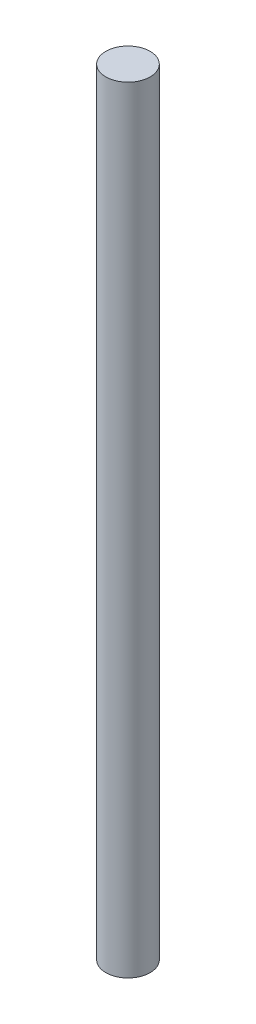
SolidWorks part; units mm, degrees
material "AISI 304"
ref_plane "Front Plane" through (0, 0, 0) normal (0, 0, 1) x (1, 0, 0)
ref_plane "Top Plane" through (0, 0, 0) normal (0, 1, 0) x (1, 0, 0)
ref_plane "Right Plane" through (0, 0, 0) normal (1, 0, 0) x (0, 0, -1)
sketch "Sketch1" plane through (0, 0, 0) normal (0, 1, 0) x (1, 0, 0)
  circle A0 centre (0, 0) radius 2
  dimension "D1" = 4
extrude "Boss-Extrude1" add sketch "Sketch1" along normal blind 70
